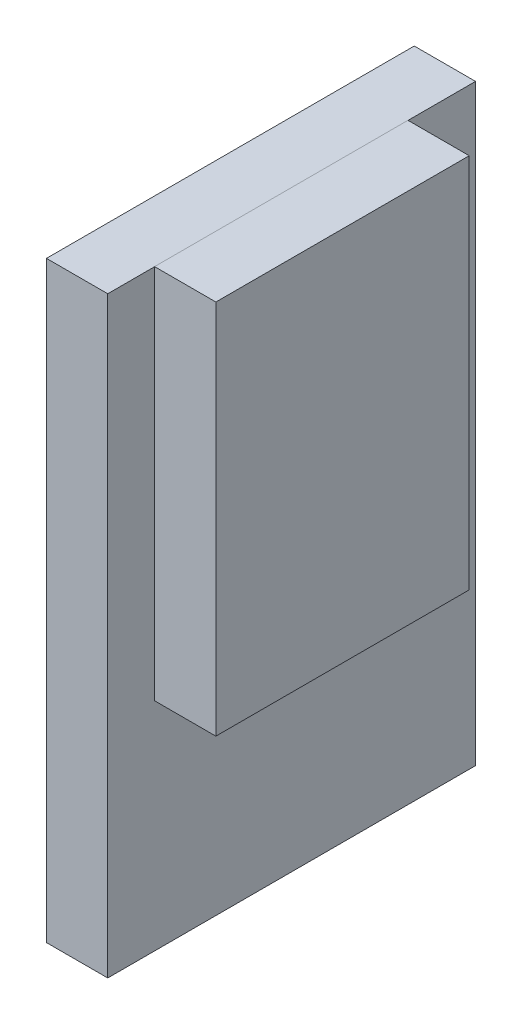
SolidWorks part; units mm, degrees
ref_plane "Front Plane" through (0, 0, 0) normal (0, 0, 1) x (1, 0, 0)
ref_plane "Top Plane" through (0, 0, 0) normal (0, 1, 0) x (1, 0, 0)
ref_plane "Right Plane" through (0, 0, 0) normal (1, 0, 0) x (0, 0, -1)
sketch "Sketch1" plane through (0, 0, 0) normal (1, 0, 0) x (0, 0, -1)
  line L0 (0, -58.42) -> (0, 0) construction
  line L1 (-39.37, 58.42) -> (39.37, 58.42)
  line L2 (-39.37, 58.42) -> (-39.37, -58.42)
  line L3 (-39.37, -58.42) -> (39.37, -58.42)
  line L4 (39.37, 58.42) -> (39.37, -58.42)
  line L5 (0, 0) -> (39.37, 0) construction
  dimension "D1" = 116.84
  dimension "D2" = 78.74
extrude "Extrude1" add sketch "Sketch1" along normal blind 19.05
sketch "Sketch4" plane through (0, -125.7596, -60.3813) normal (-1, 0, 0) x (0, 0, 1)
  line L1 (114.3, 0) -> (0, 0)
  line L2 (114.3, 0) -> (114.3, 184.15)
  line L3 (114.3, 184.15) -> (0, 184.15)
  line L4 (0, 0) -> (0, 184.15)
extrude "Boss-Extrude1" add sketch "Sketch4" along normal blind 19.05
